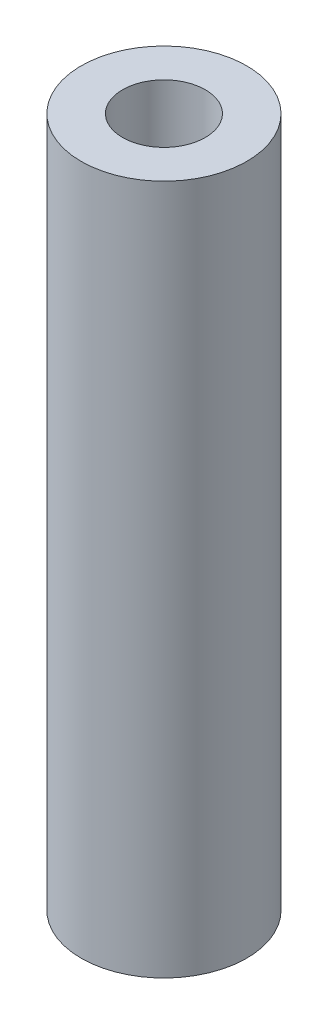
SolidWorks part; units mm, degrees
ref_plane "Front Plane" through (0, 0, 0) normal (0, 0, 1) x (1, 0, 0)
ref_plane "Top Plane" through (0, 0, 0) normal (0, 1, 0) x (1, 0, 0)
ref_plane "Right Plane" through (0, 0, 0) normal (1, 0, 0) x (0, 0, -1)
sketch "Sketch1" plane through (0, 0, 0) normal (0, 1, 0) x (1, 0, 0)
  circle A0 centre (0, 0) radius 3
  circle A1 centre (0, 0) radius 1.5
  dimension "D1" = 6
  dimension "D2" = 3
extrude "Boss-Extrude1" add sketch "Sketch1" along normal blind 25
